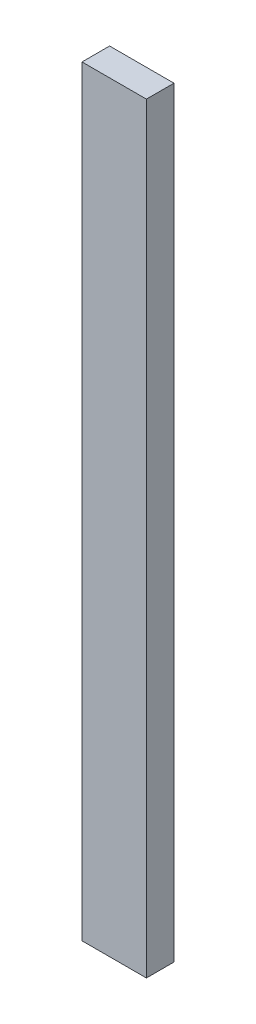
SolidWorks part; units mm, degrees
material "Oak"
ref_plane "Front Plane" through (0, 0, 0) normal (0, 0, 1) x (1, 0, 0)
ref_plane "Top Plane" through (0, 0, 0) normal (0, 1, 0) x (1, 0, 0)
ref_plane "Right Plane" through (0, 0, 0) normal (1, 0, 0) x (0, 0, -1)
sketch "Sketch1" plane through (0, 0, 0) normal (0, 1, 0) x (1, 0, 0)
  line L1 (-44.45, -19.05) -> (44.45, -19.05)
  line L2 (-44.45, -19.05) -> (-44.45, 19.05)
  line L3 (-44.45, 19.05) -> (44.45, 19.05)
  line L4 (44.45, -19.05) -> (44.45, 19.05)
  line L5 (-44.45, -19.05) -> (44.45, 19.05) construction
  line L6 (-44.45, 19.05) -> (44.45, -19.05) construction
  point P0 (0, 0)
  dimension "D1" = 38.1
  dimension "D2" = 88.9
extrude "Boss-Extrude1" add sketch "Sketch1" along normal blind 1050.925 contours L3 L4 L1 L2
